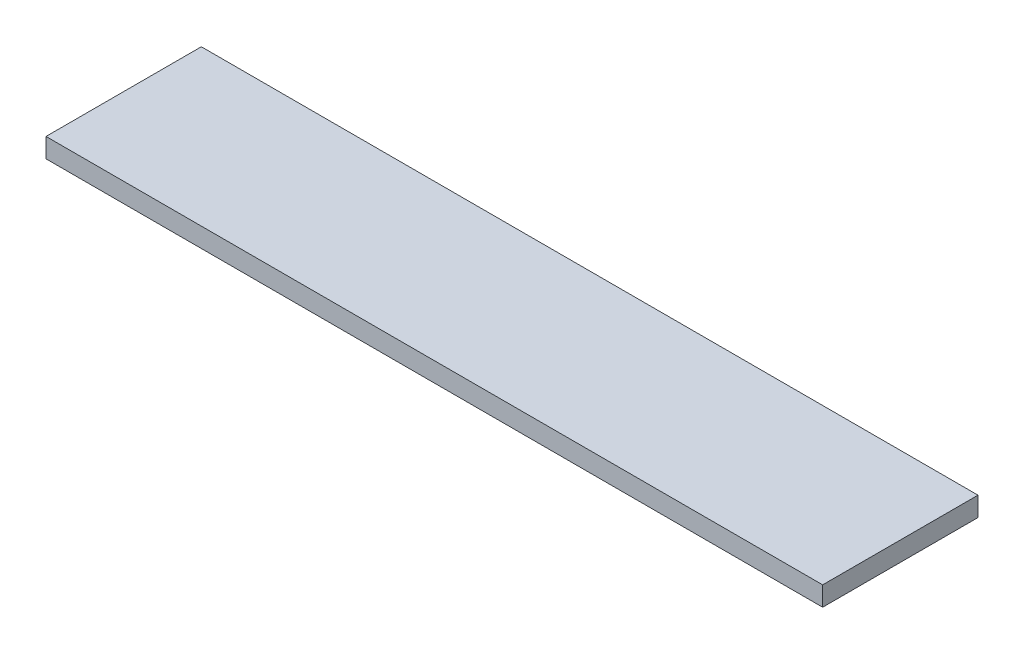
SolidWorks part; units mm, degrees
ref_plane "Front Plane" through (0, 0, 0) normal (0, 0, 1) x (1, 0, 0)
ref_plane "Top Plane" through (0, 0, 0) normal (0, 1, 0) x (1, 0, 0)
ref_plane "Right Plane" through (0, 0, 0) normal (1, 0, 0) x (0, 0, -1)
sketch "Sketch1" plane through (0, 0, 0) normal (0, 1, 0) x (1, 0, 0)
  line L1 (0, 0) -> (254, 0)
  line L2 (0, 0) -> (0, 50.8)
  line L3 (0, 50.8) -> (254, 50.8)
  line L4 (254, 0) -> (254, 50.8)
  dimension "D1" = 254
  dimension "D2" = 50.8
extrude "Boss-Extrude1" add sketch "Sketch1" along normal blind 6.35
